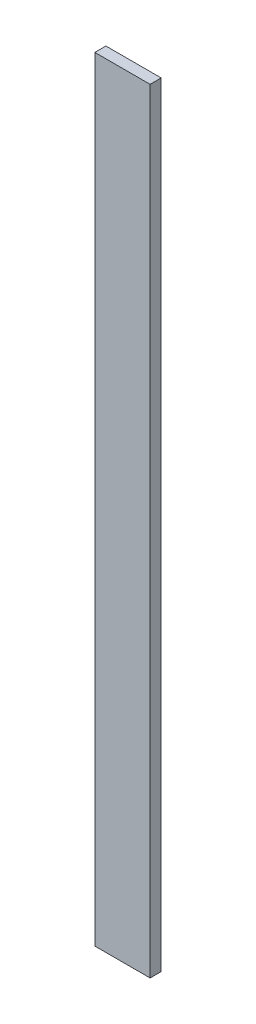
SolidWorks part; units mm, degrees
material "1.4301 (X5CrNi18-10)"
ref_plane "Ebene vorne" through (0, 0, 0) normal (0, 0, 1) x (1, 0, 0)
ref_plane "Ebene oben" through (0, 0, 0) normal (0, 1, 0) x (1, 0, 0)
ref_plane "Ebene rechts" through (0, 0, 0) normal (1, 0, 0) x (0, 0, -1)
sketch "Skizze2" plane through (0, 0, 0) normal (0, 1, 0) x (1, 0, 0)
  line L0 (43.8259, 0) -> (63.8259, 0) construction
  line L1 (36.3259, 0) -> (61.3259, 0)
  line L2 (36.3259, 0) -> (36.3259, -5)
  line L3 (36.3259, -5) -> (61.3259, -5)
  line L4 (61.3259, 0) -> (61.3259, -5)
  line L5 (33.8259, 0) -> (33.8259, 2.5) construction
  dimension "D1" = 25
  dimension "D2" = 5
  dimension "D3" = 2.5
extrude "Aufsatz-Linear austragen1" add sketch "Skizze2" along normal mid plane 350
